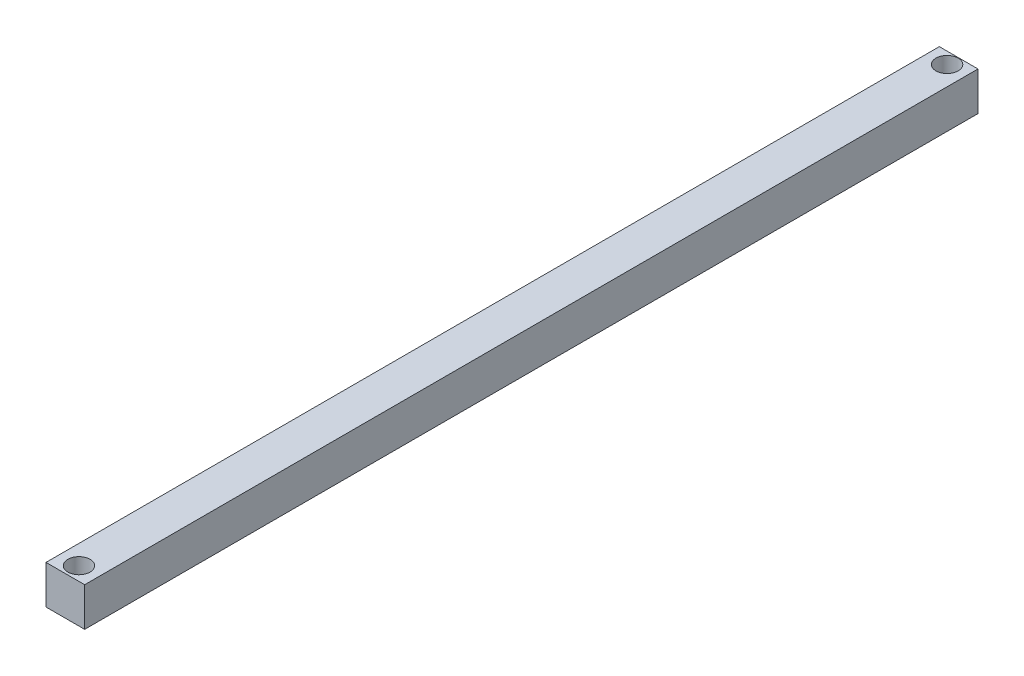
SolidWorks part; units mm, degrees
ref_plane "Front Plane" through (0, 0, 0) normal (0, 0, 1) x (1, 0, 0)
ref_plane "Top Plane" through (0, 0, 0) normal (0, 1, 0) x (1, 0, 0)
ref_plane "Right Plane" through (0, 0, 0) normal (1, 0, 0) x (0, 0, -1)
sketch "Sketch1" plane through (0, 0, 0) normal (0, 1, 0) x (1, 0, 0)
  line L1 (-10, 231) -> (10, 231)
  line L2 (-10, 231) -> (-10, -231)
  line L3 (-10, -231) -> (10, -231)
  line L4 (10, 231) -> (10, -231)
  line L5 (-10, 231) -> (10, -231) construction
  line L6 (-10, -231) -> (10, 231) construction
  point P0 (0, 0)
  dimension "D1" = 20
  dimension "D2" = 462
extrude "Boss-Extrude1" add sketch "Sketch1" along normal blind 20
sketch "Sketch3" plane through (0, 20, 0) normal (0, 1, 0) x (1, 0, 0)
  line L0 (10, 231) -> (-10, 231) construction
  line L1 (10, -231) -> (10, 231) construction
  line L2 (0, 225) -> (0, -223.96) construction
  circle A0 centre (0, 225) radius 5.75
  circle A1 centre (0, -223.96) radius 5.75
  dimension "D1" = 11.5
  dimension "D5" = 11.5
  dimension "D2" = 6
  dimension "D3" = 10
  dimension "D4" = 448.96
extrude "Cut-Extrude1" cut sketch "Sketch3" against normal through all
